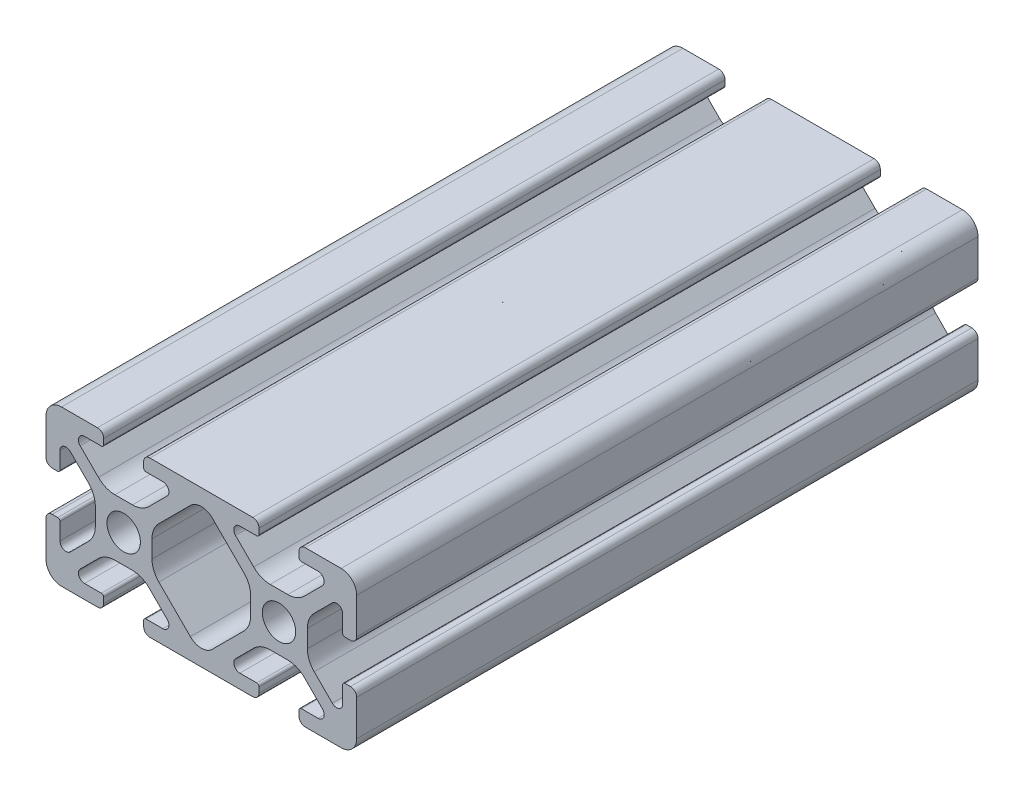
SolidWorks part; units mm, degrees
ref_plane "Alzado" through (0, 0, 0) normal (0, 0, 1) x (1, 0, 0)
ref_plane "Planta" through (0, 0, 0) normal (0, 1, 0) x (1, 0, 0)
ref_plane "Vista lateral" through (0, 0, 0) normal (1, 0, 0) x (0, 0, -1)
sketch "Croquis3" plane through (0, 0, 0) normal (0, 0, 1) x (1, 0, 0)
  line L0 (0, 15.6545) -> (0, -16.0186) construction
  line L1 (-10, 0) -> (30, 0) construction
  line L2 (-2.5748, 9.2) -> (-2.5748, 8.5)
  line L3 (-1.135, 3.65) -> (1.135, 3.65)
  line L4 (0, 0) -> (-11.6348, 11.6348) construction
  line L5 (5.5963, 6.8684) -> (3.2557, 4.528)
  line L6 (11.616, 11.6147) -> (-5.5644, -5.5638) construction
  line L7 (2.8748, 8.2) -> (5.0448, 8.2)
  line L8 (2.5748, 9.2) -> (2.5748, 8.5)
  line L9 (3.3748, 10) -> (16.6252, 10)
  line L10 (-2.8748, 8.2) -> (-5.0448, 8.2)
  line L11 (-5.5963, 6.8684) -> (-3.2557, 4.528)
  line L12 (-3.3748, 10) -> (-8, 10)
  line L13 (-6.8684, 5.5963) -> (-4.528, 3.2557)
  line L14 (-8.2, 2.8748) -> (-8.2, 5.0448)
  line L15 (-9.2, 2.5748) -> (-8.5, 2.5748)
  line L16 (-10, 3.3748) -> (-10, 8)
  line L17 (-10, -3.3748) -> (-10, -8)
  line L18 (-9.2, -2.5748) -> (-8.5, -2.5748)
  line L19 (-8.2, -2.8748) -> (-8.2, -5.0448)
  line L20 (-6.8684, -5.5963) -> (-4.528, -3.2557)
  line L21 (-3.3748, -10) -> (-8, -10)
  line L22 (-5.5963, -6.8684) -> (-3.2557, -4.528)
  line L23 (-2.8748, -8.2) -> (-5.0448, -8.2)
  line L24 (3.3748, -10) -> (16.6252, -10)
  line L25 (2.5748, -9.2) -> (2.5748, -8.5)
  line L26 (2.8748, -8.2) -> (5.0448, -8.2)
  line L27 (5.5963, -6.8684) -> (3.2557, -4.528)
  line L28 (-1.135, -3.65) -> (1.135, -3.65)
  line L29 (-2.5748, -9.2) -> (-2.5748, -8.5)
  line L30 (-3.65, 1.135) -> (-3.65, -1.135)
  line L31 (4.5284, 3.2552) -> (8.5864, 7.3147)
  line L32 (10, -13.0442) -> (10, 15.6545) construction
  line L33 (4.5284, -3.2552) -> (8.5864, -7.3147)
  line L34 (3.6501, 1.1346) -> (3.6501, -1.1346)
  line L35 (16.3499, 1.1346) -> (16.3499, -1.1346)
  line L36 (15.4716, -3.2552) -> (11.4136, -7.3147)
  line L37 (15.4716, 3.2552) -> (11.4136, 7.3147)
  line L38 (23.65, 1.135) -> (23.65, -1.135)
  line L39 (22.5748, -9.2) -> (22.5748, -8.5)
  line L40 (21.135, -3.65) -> (18.865, -3.65)
  line L41 (14.4037, -6.8684) -> (16.7443, -4.528)
  line L42 (17.1252, -8.2) -> (14.9552, -8.2)
  line L43 (17.4252, -9.2) -> (17.4252, -8.5)
  line L44 (22.8748, -8.2) -> (25.0448, -8.2)
  line L45 (25.5963, -6.8684) -> (23.2557, -4.528)
  line L46 (23.3748, -10) -> (28, -10)
  line L47 (26.8684, -5.5963) -> (24.528, -3.2557)
  line L48 (28.2, -2.8748) -> (28.2, -5.0448)
  line L49 (29.2, -2.5748) -> (28.5, -2.5748)
  line L50 (30, -3.3748) -> (30, -8)
  line L51 (30, 3.3748) -> (30, 8)
  line L52 (29.2, 2.5748) -> (28.5, 2.5748)
  line L53 (28.2, 2.8748) -> (28.2, 5.0448)
  line L54 (26.8684, 5.5963) -> (24.528, 3.2557)
  line L55 (23.3748, 10) -> (28, 10)
  line L56 (25.5963, 6.8684) -> (23.2557, 4.528)
  line L57 (22.8748, 8.2) -> (25.0448, 8.2)
  line L58 (17.4252, 9.2) -> (17.4252, 8.5)
  line L59 (17.1252, 8.2) -> (14.9552, 8.2)
  line L60 (14.4037, 6.8684) -> (16.7443, 4.528)
  line L61 (21.135, 3.65) -> (18.865, 3.65)
  line L62 (22.5748, 9.2) -> (22.5748, 8.5)
  circle A0 centre (0, 0) radius 2.15
  arc A1 (1.135, 3.65) -> (3.2557, 4.528) centre (1.135, 6.65) ccw
  arc A2 (5.5963, 6.8684) -> (5.0448, 8.2) centre (5.0448, 7.42) ccw
  arc A3 (2.8748, 8.2) -> (2.5748, 8.5) centre (2.8748, 8.5) cw
  arc A4 (2.5748, 9.2) -> (3.3748, 10) centre (3.3748, 9.2) cw
  arc A5 (-2.5748, 9.2) -> (-3.3748, 10) centre (-3.3748, 9.2) ccw
  arc A6 (-2.8748, 8.2) -> (-2.5748, 8.5) centre (-2.8748, 8.5) ccw
  arc A7 (-5.5963, 6.8684) -> (-5.0448, 8.2) centre (-5.0448, 7.42) cw
  arc A8 (-1.135, 3.65) -> (-3.2557, 4.528) centre (-1.135, 6.65) cw
  arc A9 (-3.65, 1.135) -> (-4.528, 3.2557) centre (-6.65, 1.135) ccw
  arc A10 (-6.8684, 5.5963) -> (-8.2, 5.0448) centre (-7.42, 5.0448) ccw
  arc A11 (-8.2, 2.8748) -> (-8.5, 2.5748) centre (-8.5, 2.8748) cw
  arc A12 (-9.2, 2.5748) -> (-10, 3.3748) centre (-9.2, 3.3748) cw
  arc A13 (-10, 8) -> (-8, 10) centre (-8, 8) cw
  arc A14 (-10, -8) -> (-8, -10) centre (-8, -8) ccw
  arc A15 (-9.2, -2.5748) -> (-10, -3.3748) centre (-9.2, -3.3748) ccw
  arc A16 (-8.2, -2.8748) -> (-8.5, -2.5748) centre (-8.5, -2.8748) ccw
  arc A17 (-6.8684, -5.5963) -> (-8.2, -5.0448) centre (-7.42, -5.0448) cw
  arc A18 (-3.65, -1.135) -> (-4.528, -3.2557) centre (-6.65, -1.135) cw
  arc A19 (-1.135, -3.65) -> (-3.2557, -4.528) centre (-1.135, -6.65) ccw
  arc A20 (-5.5963, -6.8684) -> (-5.0448, -8.2) centre (-5.0448, -7.42) ccw
  arc A21 (-2.8748, -8.2) -> (-2.5748, -8.5) centre (-2.8748, -8.5) cw
  arc A22 (-2.5748, -9.2) -> (-3.3748, -10) centre (-3.3748, -9.2) cw
  arc A23 (2.5748, -9.2) -> (3.3748, -10) centre (3.3748, -9.2) ccw
  arc A24 (2.8748, -8.2) -> (2.5748, -8.5) centre (2.8748, -8.5) ccw
  arc A25 (5.5963, -6.8684) -> (5.0448, -8.2) centre (5.0448, -7.42) cw
  arc A26 (1.135, -3.65) -> (3.2557, -4.528) centre (1.135, -6.65) cw
  arc A27 (3.6501, 1.1346) -> (4.5284, 3.2552) centre (6.6501, 1.1343) cw
  arc A28 (8.5864, 7.3147) -> (10, 7.9008) centre (10.0009, 5.9008) cw
  arc A29 (8.5864, -7.3147) -> (11.4136, -7.3147) centre (10, -5.9017) ccw
  arc A30 (3.6501, -1.1346) -> (4.5284, -3.2552) centre (6.6501, -1.1343) ccw
  arc A31 (29.2, -2.5748) -> (30, -3.3748) centre (29.2, -3.3748) cw
  arc A32 (16.3499, -1.1346) -> (15.4716, -3.2552) centre (13.3499, -1.1343) cw
  arc A34 (11.4136, 7.3147) -> (10, 7.9008) centre (9.9991, 5.9008) ccw
  arc A35 (16.3499, 1.1346) -> (15.4716, 3.2552) centre (13.3499, 1.1343) ccw
  arc A36 (18.865, -3.65) -> (16.7443, -4.528) centre (18.865, -6.65) ccw
  arc A37 (14.4037, -6.8684) -> (14.9552, -8.2) centre (14.9552, -7.42) ccw
  arc A38 (17.1252, -8.2) -> (17.4252, -8.5) centre (17.1252, -8.5) cw
  arc A39 (17.4252, -9.2) -> (16.6252, -10) centre (16.6252, -9.2) cw
  arc A40 (22.5748, -9.2) -> (23.3748, -10) centre (23.3748, -9.2) ccw
  arc A41 (22.8748, -8.2) -> (22.5748, -8.5) centre (22.8748, -8.5) ccw
  arc A42 (25.5963, -6.8684) -> (25.0448, -8.2) centre (25.0448, -7.42) cw
  arc A43 (21.135, -3.65) -> (23.2557, -4.528) centre (21.135, -6.65) cw
  arc A44 (23.65, -1.135) -> (24.528, -3.2557) centre (26.65, -1.135) ccw
  arc A45 (26.8684, -5.5963) -> (28.2, -5.0448) centre (27.42, -5.0448) ccw
  arc A46 (28.2, -2.8748) -> (28.5, -2.5748) centre (28.5, -2.8748) cw
  arc A47 (30, -8) -> (28, -10) centre (28, -8) cw
  arc A48 (30, 8) -> (28, 10) centre (28, 8) ccw
  arc A49 (29.2, 2.5748) -> (30, 3.3748) centre (29.2, 3.3748) ccw
  arc A50 (28.2, 2.8748) -> (28.5, 2.5748) centre (28.5, 2.8748) ccw
  arc A51 (26.8684, 5.5963) -> (28.2, 5.0448) centre (27.42, 5.0448) cw
  arc A52 (23.65, 1.135) -> (24.528, 3.2557) centre (26.65, 1.135) cw
  arc A53 (21.135, 3.65) -> (23.2557, 4.528) centre (21.135, 6.65) ccw
  arc A54 (25.5963, 6.8684) -> (25.0448, 8.2) centre (25.0448, 7.42) ccw
  arc A55 (22.8748, 8.2) -> (22.5748, 8.5) centre (22.8748, 8.5) cw
  arc A56 (22.5748, 9.2) -> (23.3748, 10) centre (23.3748, 9.2) cw
  arc A57 (17.4252, 9.2) -> (16.6252, 10) centre (16.6252, 9.2) ccw
  arc A58 (17.1252, 8.2) -> (17.4252, 8.5) centre (17.1252, 8.5) ccw
  arc A59 (14.4037, 6.8684) -> (14.9552, 8.2) centre (14.9552, 7.42) cw
  arc A60 (18.865, 3.65) -> (16.7443, 4.528) centre (18.865, 6.65) cw
  circle A61 centre (20, 0) radius 2.15
  point P23 (20, -3.65)
  point P36 (0, 3.65)
  point P90 (10, 10)
  point P91 (0, -3.65)
  point P197 (20, 3.65)
  dimension "D1" = 4.3
  dimension "D5" = 3
  dimension "D9" = 0.78
  dimension "D11" = 0.3
  dimension "D14" = 0.8
  dimension "D17" = 2
  dimension "D20" = 2
  dimension "D2" = 1.135
  dimension "D3" = 3.65
  dimension "D4" = 0.9
  dimension "D6" = 3.31
  dimension "D7" = 8.2
  dimension "D8" = 2.17
  dimension "D12" = 0.7
  dimension "D13" = 13.2504
  dimension "D18" = 5.74
  dimension "D19" = 10
extrude "Saliente-Extruir1" add sketch "Croquis3" along normal blind 80
